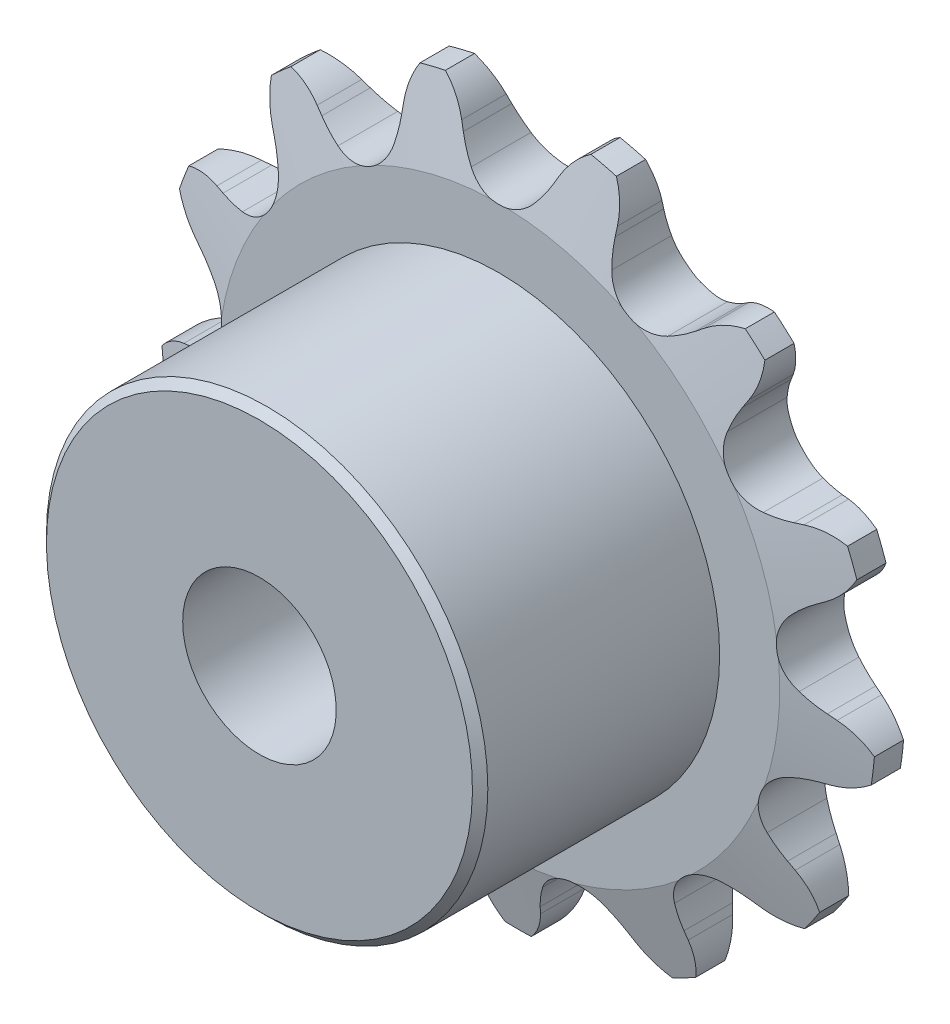
SolidWorks part; units mm, degrees
ref_plane "Front Plane" through (0, 0, 0) normal (0, 0, 1) x (1, 0, 0)
ref_plane "Top Plane" through (0, 0, 0) normal (0, 1, 0) x (1, 0, 0)
ref_plane "Right Plane" through (0, 0, 0) normal (1, 0, 0) x (0, 0, -1)
sketch "Sketch0" plane through (0, 0, 0) normal (0, 0, 1) x (1, 0, 0)
  line L0 (3.175, -12.8815) -> (0, 0) construction
  line L1 (0, 0) -> (8.7976, -9.9305) construction
  line L2 (0, 0) -> (-3.175, -12.8815) construction
  line L3 (3.175, -12.8815) -> (8.7976, -9.9305) construction
  line L4 (3.175, -12.8815) -> (-3.175, -12.8815) construction
  line L5 (5.1561, -12.4911) -> (4.9373, -12.2283)
  line L6 (3.175, -12.8815) -> (0, -13.664) construction
  line L7 (1.2394, -13.4564) -> (1.311, -13.1221)
  line L8 (0, -12.8815) -> (0, -14.7865) construction
  line L9 (4.1855, -11.5177) -> (1.6023, -15.0039) construction
  line L10 (0, 0) -> (0, -12.8815) construction
  line L11 (4.9373, -12.2283) -> (1.6023, -15.0039) construction
  line L12 (0, -14.7865) -> (0, -15.2172) construction
  line L13 (7.2683, -10.7332) -> (5.1561, -12.4911) construction
  circle A0 centre (0, 0) radius 14.7865 construction
  circle A1 centre (0, 0) radius 13.267 construction
  arc A2 (-1.7547, -15.6123) -> (8.8092, -13.0086) centre (0, 0) ccw
  circle A3 centre (0, 0) radius 15.2172 construction
  circle A4 centre (3.175, -12.8815) radius 1.651 construction
  arc A7 (4.1855, -11.5177) -> (1.6464, -12.1436) centre (3.175, -12.8815) ccw
  circle A8 centre (3.175, -12.8815) radius 1.6974 construction
  arc A9 (5.1561, -12.4911) -> (8.8092, -13.0086) centre (7.2683, -10.7332) ccw
  arc A10 (4.9373, -12.2283) -> (4.1855, -11.5177) centre (1.6023, -15.0039) ccw
  arc A11 (1.2394, -13.4564) -> (-1.7547, -15.6123) centre (-1.4478, -12.8815) cw
  arc A12 (1.311, -13.1221) -> (1.6464, -12.1436) centre (5.5539, -14.0299) cw
  dimension "D1" = 1.6974
  dimension "Dr" = 3.302
  dimension "Ds" = 3.3947
  dimension "R" = 1.6974
  dimension "Pitch" = 6.35
  dimension "A" = 39.615
  dimension "360/N" = 27.692
  dimension "B" = 13.692
  dimension "ab" = 4.6228
  dimension "J" = 1.905
  dimension "ac" = 2.6416
sketch "Sketch1" plane through (0, 0, 0) normal (1, 0, 0) x (0, 0, -1)
  line L0 (1.397, 0) -> (-1.397, 0)
  line L1 (-1.397, 0) -> (-1.397, 11.6115)
  line L2 (-1.397, 11.6115) -> (-0.6033, 14.7865)
  line L3 (-0.6033, 14.7865) -> (0.6033, 14.7865)
  line L4 (0.6033, 14.7865) -> (1.397, 11.6115)
  line L5 (1.397, 11.6115) -> (1.397, 0)
  line L7 (0, 14.7865) -> (0, 0) construction
  line L8 (-1.397, 11.6115) -> (1.397, 11.6115) construction
  line L9 (0, 14.7865) -> (0, -14.7865) construction
  line L10 (-1.397, 11.6115) -> (-1.397, 14.7865) construction
  line L11 (-1.397, 14.7865) -> (-0.6033, 14.7865) construction
  line L12 (0.6033, 14.7865) -> (1.397, 14.7865) construction
  line L13 (1.397, 14.7865) -> (1.397, 11.6115) construction
  line L14 (0, 0) -> (-6.4008, 0) construction
  line L22 (1.397, 0) -> (-11.303, 0) construction
  line L24 (-1.397, 0) -> (-1.397, 9.3255) construction
  dimension "t" = 2.794
  dimension "g" = 0.7937
  dimension "h" = 3.175
  dimension "K" = 6.4008
  dimension "MHD" = 18.651
  dimension "Width" = 12.7
revolve "Revolve1" add sketch "Sketch1" angle 360 mid plane about L0
extrude "Cut-Extrude1" cut sketch "Sketch0" against normal through all and the other way through all
pattern_circular "CirPattern1" count 13 over 360 about axis through (0, 0, 0) along (0, 0, 1) of "Cut-Extrude1"
sketch "Sketch2" plane through (0, 0, 0) normal (0, 0, 1) x (1, 0, 0)
  circle A0 centre (0, 0) radius 3.175 construction
  circle A1 centre (0, 0) radius 9.1281
  circle A2 centre (0, 0) radius 14.859 construction
  dimension "Bore" = 6.35
  dimension "Hub Dia." = 18.2562
  dimension "OD" = 29.718
extrude "Boss-Extrude1" add sketch "Sketch2" along normal up to vertex (11.303 mm away) from surface at 1.397 starting at face at (0, 0, 1.397)
sketch "Sketch3" plane through (0, 0, 0) normal (0, 0, 1) x (1, 0, 0)
  circle A0 centre (0, 0) radius 3.175 construction
  circle A1 centre (0, 0) radius 3.175
extrude "Cut-Extrude2" cut sketch "Sketch3" along normal through all and the other way through all
sketch "Sketch4" plane through (0, 0, 0) normal (1, 0, 0) x (0, 0, -1)
  line L0 (-11.303, 9.1281) -> (-11.303, 8.8106)
  line L1 (-1.397, 14.7865) -> (-3.4925, 14.7865)
  line L2 (-1.397, 14.7865) -> (-1.397, 9.3255)
  line L3 (-1.397, 9.3255) -> (-3.4925, 9.3255)
  line L4 (-3.4925, 14.7865) -> (-3.4925, 9.3255)
  line L9 (-11.303, 8.8106) -> (-10.9855, 9.1281)
  line L10 (-10.9855, 9.1281) -> (-11.303, 9.1281)
  dimension "C" = 0.3175
  dimension "D3" = 2.0955
revolve "Cut-Revolve1" cut sketch "Sketch4" angle 360 mid plane about L22
equation "\"360/N@Sketch0\" = 360/\"Teeth@CirPattern1\""
equation "\"Ds@Sketch0\" = 1.005 * \"Dr@Sketch0\" + 0.003"
equation "\"R@Sketch0\" = 1/2 * \"Ds@Sketch0\""
equation "\"A@Sketch0\" = 35 +  ( 60 / \"Teeth@CirPattern1\" ) "
equation "\"B@Sketch0\" = 18 -  ( 56 / \"Teeth@CirPattern1\" )"
equation "\"ac@Sketch0\" = 0.8 * \"Dr@Sketch0\""
equation "\"ab@Sketch0\" = 1.4 * \"Dr@Sketch0\""
equation "\"J@Sketch0\" = 0.3 * \"Pitch@Sketch0\""
equation "\"h@Sketch1\" = \"Pitch@Sketch0\" / 2"
equation "\"g@Sketch1\" = \"h@Sketch1\" / 4"
equation "\"MHD@Sketch1\" = \"Pitch@Sketch0\" * ( cotan ( 180 / \"Teeth@CirPattern1\" ) - 1 ) - 0.030"
equation "\"D3@Sketch4\" = \"t@Sketch1\" * 3 / 4"
